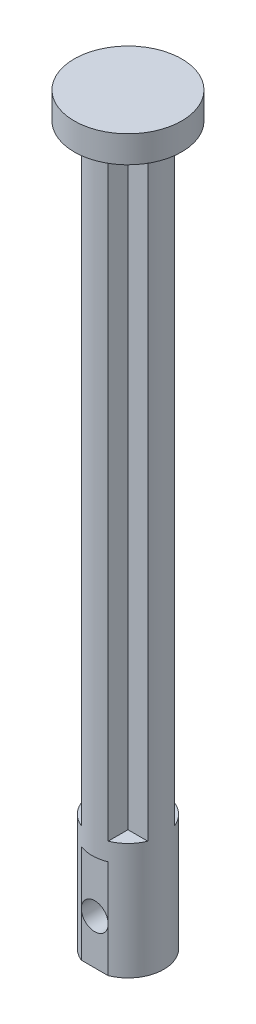
SolidWorks part; units mm, degrees
ref_plane "Front Plane" through (0, 0, 0) normal (0, 0, 1) x (1, 0, 0)
ref_plane "Top Plane" through (0, 0, 0) normal (0, 1, 0) x (1, 0, 0)
ref_plane "Right Plane" through (0, 0, 0) normal (1, 0, 0) x (0, 0, -1)
sketch "Sketch1" plane through (0, 0, 0) normal (0, 1, 0) x (1, 0, 0)
  circle A0 centre (0, 0) radius 4
  dimension "D1" = 8
extrude "Boss-Extrude1" add sketch "Sketch1" along normal blind 80
sketch "Sketch2" plane through (0, 0, 0) normal (0, -1, 0) x (1, 0, 0)
  line L0 (-1.5, 3.7081) -> (1.5, 3.7081)
  arc A0 (1.5, 3.7081) -> (-1.5, 3.7081) centre (0, 0) ccw
  point P5 (0, 3.7081)
  dimension "D2" = 8
  dimension "D1" = 3
extrude "Cut-Extrude1" cut sketch "Sketch2" against normal blind 11
sketch "Sketch3" plane through (0, 0, 3.7081) normal (0, 0, 1) x (1, 0, 0)
  circle A0 centre (0, 5) radius 1.5
  dimension "D2" = 3
  dimension "D1" = 5
extrude "Cut-Extrude2" cut sketch "Sketch3" against normal blind 4
sketch "Sketch4" plane through (0, 80, 0) normal (0, 1, 0) x (1, 0, 0)
  line L2 (-1.5, -3.5864) -> (-1.5, -3.7081)
  line L4 (-3.7081, -1.5) -> (-1.5, -1.5)
  line L5 (-1.5, -1.5) -> (-1.5, -3.5864)
  line L6 (-3.7081, 1.5) -> (-1.5, 1.5)
  line L7 (-1.5, 1.5) -> (-1.5, 3.7081)
  line L8 (1.5, 3.7081) -> (1.5, 1.5)
  line L9 (1.5, 1.5) -> (3.7081, 1.5)
  line L10 (1.5, -3.7081) -> (1.5, -1.5)
  line L11 (1.5, -1.5) -> (3.7081, -1.5)
  arc A0 (1.5, -3.7081) -> (3.7081, -1.5) centre (0, 0) ccw
  arc A1 (-3.7081, -1.5) -> (-1.5, -3.7081) centre (0, 0) ccw
  arc A2 (-1.5, 3.7081) -> (-3.7081, 1.5) centre (0, 0) ccw
  arc A3 (3.7081, 1.5) -> (1.5, 3.7081) centre (0, 0) ccw
  dimension "D1" = 8
  dimension "D2" = 3
  dimension "D3" = 3
  dimension "D4" = 3
  dimension "D5" = 3
extrude "Cut-Extrude3" cut sketch "Sketch4" against normal blind 67
sketch "Sketch5" plane through (0, 80, 0) normal (0, 1, 0) x (1, 0, 0)
  circle A0 centre (0, 0) radius 6
  dimension "D1" = 12
extrude "Boss-Extrude2" add sketch "Sketch5" along normal blind 3
